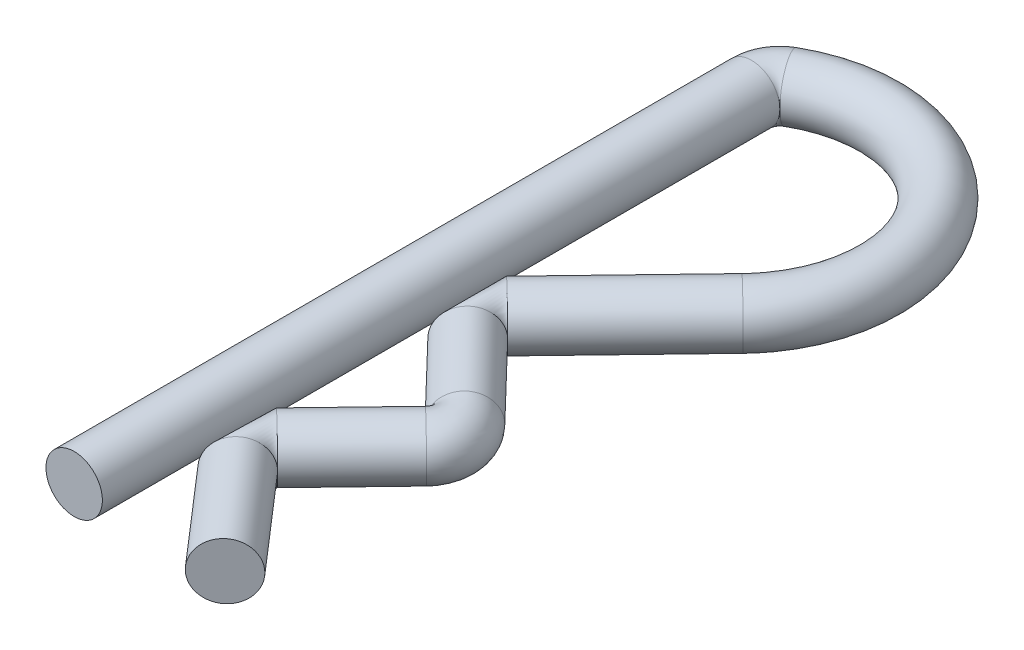
SolidWorks part; units mm, degrees
ref_plane "Front Plane" through (0, 0, 0) normal (0, 0, 1) x (1, 0, 0)
ref_plane "Top Plane" through (0, 0, 0) normal (0, 1, 0) x (1, 0, 0)
ref_plane "Right Plane" through (0, 0, 0) normal (1, 0, 0) x (0, 0, -1)
sketch "Sketch1" plane through (0, 0, 0) normal (0, 1, 0) x (1, 0, 0)
  line L0 (0, 0) -> (0, 12)
  line L1 (3.3017, 8.5348) -> (1.2565, 6.4087)
  line L2 (1.2565, 5.7154) -> (2.5334, 4.388)
  line L3 (2.5334, 3.6947) -> (1.2395, 2.3496)
  line L4 (1.2219, 1.6757) -> (2.6731, 0)
  line L5 (0.9231, 6.062) -> (0.9231, 2.0207) construction
  line L7 (0.9231, 2.0207) -> (0.9231, -2.0207) construction
  line L8 (2.6731, 0) -> (0.9231, 0) construction
  arc A0 (3.3017, 8.5348) -> (0.25, 12.433) centre (1.5, 10.2679) ccw
  arc A1 (1.2395, 2.3496) -> (1.2219, 1.6757) centre (1.5998, 2.003) ccw
  arc A2 (2.5334, 4.388) -> (2.5334, 3.6947) centre (2.1731, 4.0414) cw
  arc A3 (1.2565, 6.4087) -> (1.2565, 5.7154) centre (1.6168, 6.062) ccw
  arc A4 (0.25, 12.433) -> (0, 12) centre (0.5, 12) ccw
  point P1 (0.2106, 12.2825)
  point P11 (0, 0)
  point P12 (0.9231, 4.0414)
  point P13 (2.6731, 4.0414)
  point P20 (2.8668, 4.0414)
  point P24 (1.1, 2.0161)
  point P25 (0, 0)
  point P27 (1.1168, 6.062)
  point P29 (0.25, 12.2575)
  dimension "D1" = 5
  dimension "D3" = 0.5
  dimension "D4" = 1.1
  dimension "D7" = 1
  dimension "D2" = 0.5
  dimension "D5" = 1.75
  dimension "D6" = 12
sweep "Sweep1" add path "Sketch1" circular profile diameter 1 parameters "D3"=1
